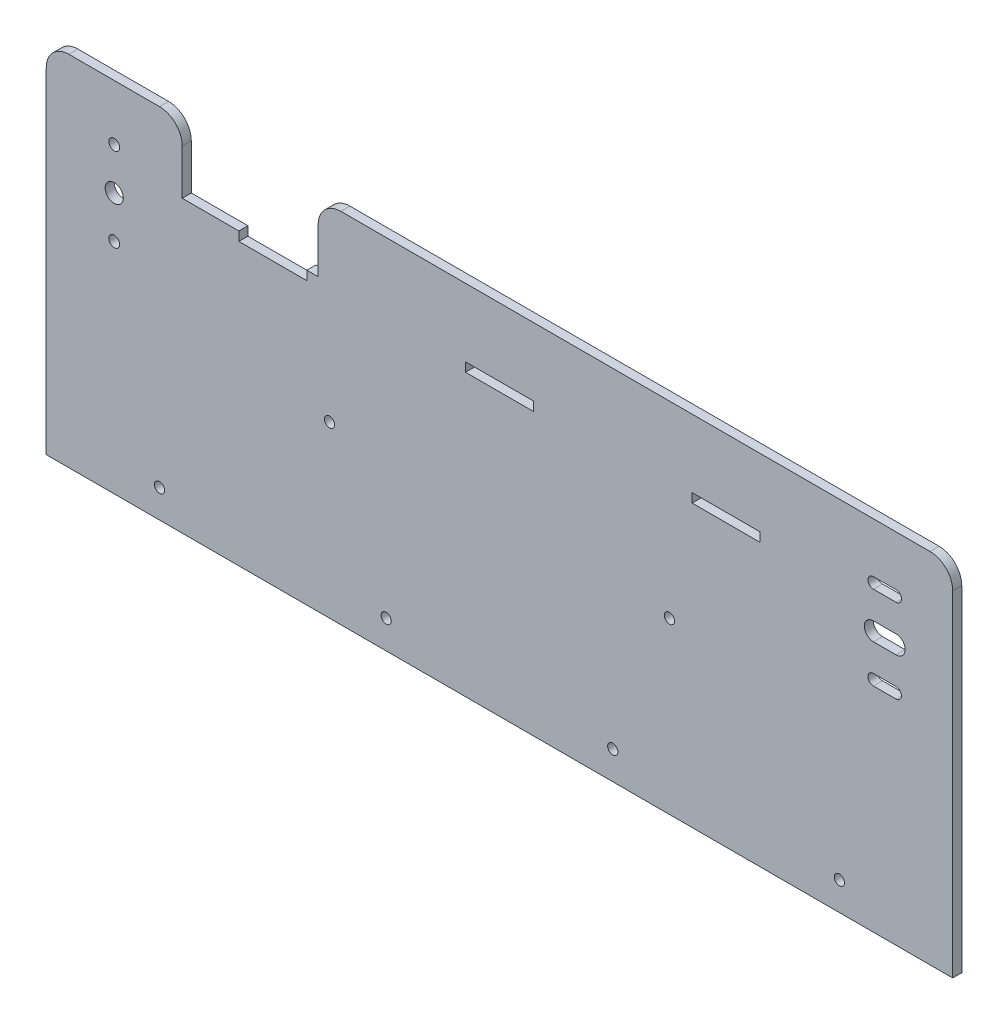
SolidWorks part; units mm, degrees
material "Acrílico (médio-alto impacto)"
ref_plane "Plano frontal" through (0, 0, 0) normal (0, 0, 1) x (1, 0, 0)
ref_plane "Plano superior" through (0, 0, 0) normal (0, 1, 0) x (1, 0, 0)
ref_plane "Plano direito" through (0, 0, 0) normal (1, 0, 0) x (0, 0, -1)
sketch "Esboço1" plane through (0, 0, 0) normal (0, 0, 1) x (1, 0, 0)
  line L0 (0, 0) -> (400, 0)
  line L2 (10, 150) -> (50, 150)
  line L3 (60, 130) -> (60, 140)
  line L4 (60, 130) -> (120, 130)
  line L5 (120, 130) -> (120, 140)
  line L6 (130, 150) -> (390, 150)
  line L7 (400, 140) -> (400, 0)
  line L8 (0, 140) -> (0, 0)
  line L9 (30, 133.5) -> (30, 96.5) construction
  line L10 (85, 126) -> (115, 126) construction
  line L11 (85, 124) -> (115, 124)
  line L12 (85, 124) -> (85, 128)
  line L13 (85, 128) -> (115, 128)
  line L14 (115, 124) -> (115, 128)
  line L15 (185, 124) -> (215, 124)
  line L16 (185, 128) -> (215, 128)
  line L17 (215, 124) -> (215, 128)
  line L18 (185, 126) -> (215, 126) construction
  line L19 (185, 124) -> (185, 128)
  line L20 (285, 124) -> (315, 124)
  line L21 (285, 128) -> (315, 128)
  line L22 (315, 124) -> (315, 128)
  line L23 (285, 126) -> (315, 126) construction
  line L24 (285, 124) -> (285, 128)
  line L61 (365, 133.5) -> (375, 133.5) construction
  line L62 (365, 135.9) -> (375, 135.9)
  line L63 (365, 131.1) -> (375, 131.1)
  line L64 (365, 96.5) -> (375, 96.5) construction
  line L67 (365, 98.9) -> (375, 98.9)
  line L68 (365, 94.1) -> (375, 94.1)
  line L69 (370, 133.5) -> (370, 96.5) construction
  circle A1 centre (30, 133.5) radius 2.4
  circle A2 centre (30, 96.5) radius 2.4
  arc A3 (60, 140) -> (50, 150) centre (50, 140) ccw
  arc A4 (390, 150) -> (400, 140) centre (390, 140) cw
  arc A5 (0, 140) -> (10, 150) centre (10, 140) cw
  arc A6 (120, 140) -> (130, 150) centre (130, 140) cw
  arc A9 (365, 135.9) -> (365, 131.1) centre (365, 133.5) ccw
  arc A10 (375, 131.1) -> (375, 135.9) centre (375, 133.5) ccw
  arc A13 (365, 98.9) -> (365, 94.1) centre (365, 96.5) ccw
  arc A14 (375, 94.1) -> (375, 98.9) centre (375, 96.5) ccw
  point P3 (30, 115)
  point P16 (60, 150)
  point P21 (0, 150)
  point P30 (200, 126)
  point P31 (370, 115)
  point P75 (370, 133.5)
  point P103 (370, 96.5)
  dimension "D6" = 37
  dimension "D7" = 4.8
  dimension "D8" = 4.8
  dimension "D11" = 10
  dimension "D12" = 10
  dimension "D19" = 35
  dimension "D20" = 200
  dimension "D34" = 2.4
  dimension "D37" = 2.4
  dimension "D1" = 400
  dimension "D2" = 150
  dimension "D3" = 60
  dimension "D4" = 20
  dimension "D5" = 60
  dimension "D9" = 35
  dimension "D10" = 30
  dimension "D13" = 4
  dimension "D14" = 30
  dimension "D15" = 2
  dimension "D17" = 70
  dimension "D18" = 30
  dimension "D33" = 10
  dimension "D35" = 37
  dimension "D36" = 10
  dimension "D16" = 3
extrude "Ressalto-extrusão1" add sketch "Esboço1" along normal blind 4
sketch "Esboço3" plane through (0, 0, 4) normal (0, 0, 1) x (1, 0, 0)
  line L0 (365, 115) -> (375, 115) construction
  line L1 (365, 119) -> (375, 119)
  line L2 (365, 111) -> (375, 111)
  line L7 (30, 133.5) -> (30, 96.5) construction
  line L8 (370, 131.1) -> (370, 98.9) construction
  line L9 (365, 131.1) -> (375, 131.1) construction
  line L10 (375, 98.9) -> (365, 98.9) construction
  arc A0 (365, 119) -> (365, 111) centre (365, 115) ccw
  arc A1 (375, 111) -> (375, 119) centre (375, 115) ccw
  circle A2 centre (30, 115) radius 4
  point P2 (370, 115)
  point P16 (370, 115)
  point P17 (30, 115)
  dimension "D2" = 4
  dimension "D5" = 8
  dimension "D1" = 10
extrude "Corte-extrusão1" cut sketch "Esboço3" against normal blind 6
hole_wizard "Furo com folga de M41" positions "3DSketch1" profile "Esboço6" hole size "M4" standard "ISO" end condition through all
sketch3d "3DSketch1"
  line L0 (0, 0, 4) -> (400, 0, 4) construction
  line L1 (50, 12.5, 4) -> (350, 12.5, 4) construction
  line L3 (0, 140, 4) -> (0, 0, 4) construction
  line L4 (400, 0, 4) -> (400, 140, 4) construction
  line L5 (125, 75, 4) -> (275, 75, 4) construction
  point P37 (125, 75, 4)
  point P40 (275, 75, 4)
  point P42 (50, 12.5, 4)
  point P44 (150, 12.5, 4)
  point P46 (250, 12.5, 4)
  point P48 (350, 12.5, 4)
  dimension "D1" = 12.5
  dimension "D2" = 50
  dimension "D3" = 50
  dimension "D4" = 100
  dimension "D5" = 100
  dimension "D6" = 125
  dimension "D7" = 125
  dimension "D8" = 75
sketch "Esboço6" plane through (350, 12.5, 4) normal (1, 0, 0) x (0, -1, 0)
  line L0 (0, 0) -> (0, 4)
  line L1 (0, 4) -> (2.25, 4)
  line L2 (2.25, 4) -> (2.25, 0)
  line L5 (2.25, 0) -> (0, 0)
  line L11 (0, -6.35) -> (0, 107.95) construction
  dimension "Thru Hole Dia." = 4.5
  dimension "Thru Hole Depth" = 4
sketch "Esboço7" plane through (0, 0, 4) normal (0, 0, 1) x (1, 0, 0)
  line L0 (115, 128) -> (85, 128) construction
  line L1 (60, 130) -> (120, 130)
  line L2 (60, 130) -> (60, 128)
  line L3 (60, 128) -> (120, 128)
  line L4 (120, 130) -> (120, 128)
extrude "Corte-extrusão4" cut sketch "Esboço7" against normal through all
sketch "Esboço8" plane through (0, 0, 4) normal (0, 0, 1) x (1, 0, 0)
  line L0 (10, 158) -> (50, 158)
  line L1 (0, 140) -> (0, 148)
  line L2 (60, 140) -> (60, 148)
  line L3 (120, 140) -> (120, 148)
  line L4 (400, 140) -> (400, 148)
  line L5 (50, 150) -> (10, 150) construction
  line L6 (50, 150) -> (10, 150)
  line L7 (390, 150) -> (130, 150) construction
  line L8 (390, 150) -> (130, 150)
  line L9 (130, 158) -> (390, 158)
  arc A0 (10, 150) -> (0, 140) centre (10, 140) ccw construction
  arc A1 (60, 140) -> (50, 150) centre (50, 140) ccw construction
  arc A2 (60, 140) -> (50, 150) centre (50, 140) ccw
  arc A3 (10, 150) -> (0, 140) centre (10, 140) ccw
  arc A4 (400, 140) -> (390, 150) centre (390, 140) ccw construction
  arc A5 (130, 150) -> (120, 140) centre (130, 140) ccw construction
  arc A6 (400, 140) -> (390, 150) centre (390, 140) ccw
  arc A7 (130, 150) -> (120, 140) centre (130, 140) ccw
  arc A8 (400, 148) -> (390, 158) centre (390, 148) ccw
  arc A9 (120, 148) -> (130, 158) centre (130, 148) cw
  arc A10 (60, 148) -> (50, 158) centre (50, 148) ccw
  arc A11 (10, 158) -> (0, 148) centre (10, 148) ccw
  point P23 (120, 158)
  dimension "D1" = 10
  dimension "D2" = 158
extrude "Ressalto-extrusão2" add sketch "Esboço8" against normal up to surface (4 mm away) up to face at (133.75, 120.5178, 0)
